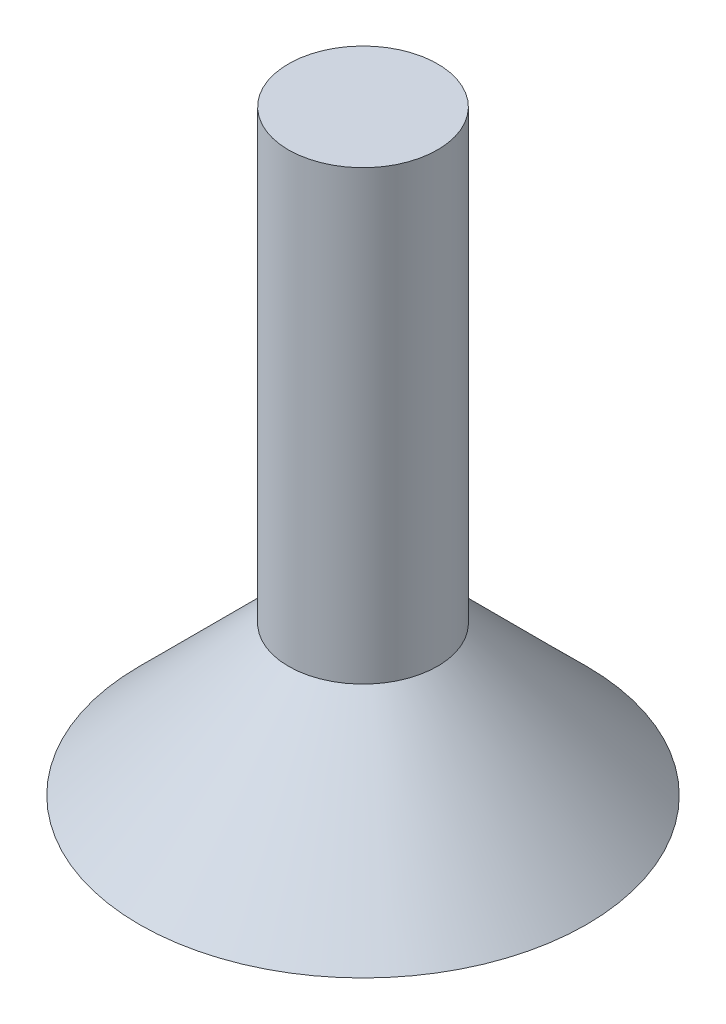
SolidWorks part; units mm, degrees
ref_plane "Front Plane" through (0, 0, 0) normal (0, 0, 1) x (1, 0, 0)
ref_plane "Top Plane" through (0, 0, 0) normal (0, 1, 0) x (1, 0, 0)
ref_plane "Right Plane" through (0, 0, 0) normal (1, 0, 0) x (0, 0, -1)
sketch "Sketch1" plane through (0, 0, 0) normal (1, 0, 0) x (0, 0, -1)
  line L1 (15, 0) -> (5, 10)
  line L2 (5, 10) -> (5, 40)
  line L4 (0, 40) -> (0, 0) construction
  line L7 (0, 0) -> (15, 0)
  line L8 (0, 40) -> (5, 40)
  line L9 (0, 0) -> (0, 40)
  dimension "D1" = 45
  dimension "D2" = 5
  dimension "D3" = 40
  dimension "D4" = 14.1421
revolve "Revolve1" add sketch "Sketch1" angle 360 about L4
